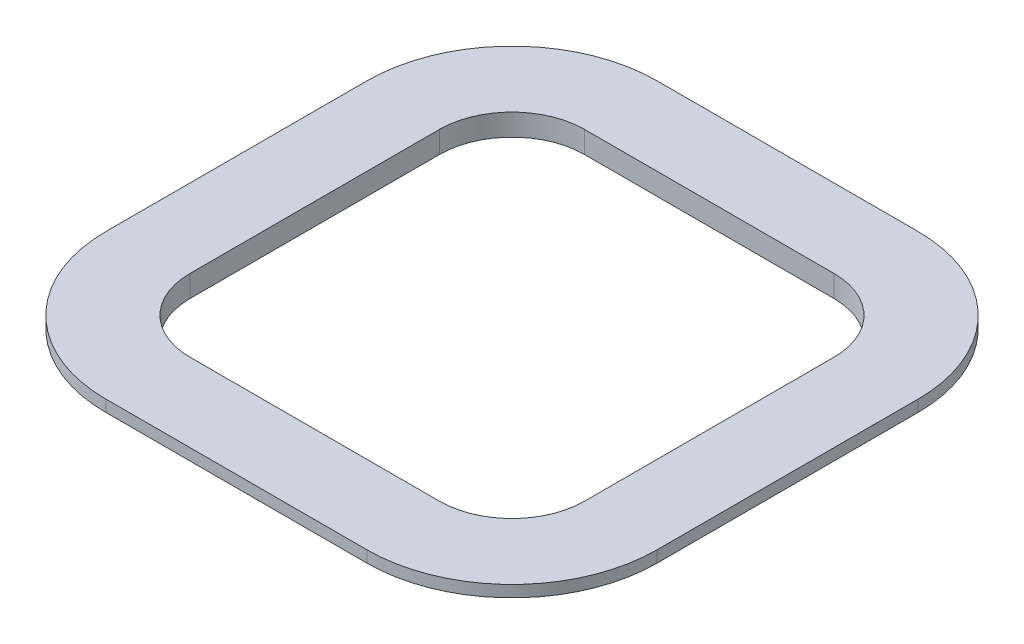
SolidWorks part; units mm, degrees
ref_plane "Front" through (0, 0, 0) normal (0, 0, 1) x (1, 0, 0)
ref_plane "Top" through (0, 0, 0) normal (0, 1, 0) x (1, 0, 0)
ref_plane "Right" through (0, 0, 0) normal (1, 0, 0) x (0, 0, -1)
sketch "Sketch1" plane through (0, 0, 0) normal (0, 1, 0) x (1, 0, 0)
  line L0 (-13.6, 13.6) -> (13.6, -13.6) construction
  line L1 (-19, 19) -> (19, 19)
  line L2 (-19, 19) -> (-19, -19)
  line L3 (-19, -19) -> (19, -19)
  line L4 (19, 19) -> (19, -19)
  line L5 (-13.6, 13.6) -> (13.6, 13.6)
  line L6 (-13.6, 13.6) -> (-13.6, -13.6)
  line L7 (-13.6, -13.6) -> (13.6, -13.6)
  line L8 (13.6, 13.6) -> (13.6, -13.6)
  line L9 (19, 19) -> (-19, -19) construction
  point P8 (0, 0)
  point P9 (0, 0)
  dimension "D1" = 38
  dimension "D2" = 27.2
extrude "Extrude1" add sketch "Sketch1" against normal blind 1.5
fillet "Fillet1" radius 5 4 edges at (13.6, -0.75, 13.6) (-13.6, -0.75, 13.6) (-13.6, -0.75, -13.6) (13.6, -0.75, -13.6)
fillet "Fillet2" radius 10 4 edges at (19, -0.75, 19) (19, -0.75, -19) (-19, -0.75, -19) (-19, -0.75, 19)
sketch "Sketch2" plane through (0, 0, 0) normal (0, 0, 1) x (1, 0, 0)
  line L0 (19, -0.8) -> (19, -1.5)
  line L1 (19, -1.5) -> (13.6, -1.5)
  line L2 (13.6, -1.5) -> (19, -0.8)
  dimension "D1" = 0.7
sketch "Sketch3" plane through (0, -1.5, 0) normal (0, -1, 0) x (1, 0, 0)
  line L4 (13.6, -8.6) -> (13.6, 8.6)
  line L5 (-8.6, -13.6) -> (8.6, -13.6)
  line L6 (-13.6, 8.6) -> (-13.6, -8.6)
  line L7 (8.6, 13.6) -> (-8.6, 13.6)
  line L8 (13.6, -8.6) -> (13.6, 8.6)
  line L9 (-8.6, -13.6) -> (8.6, -13.6)
  line L10 (-13.6, 8.6) -> (-13.6, -8.6)
  line L11 (8.6, 13.6) -> (-8.6, 13.6)
  arc A4 (8.6, -13.6) -> (13.6, -8.6) centre (8.6, -8.6) ccw
  arc A5 (-13.6, -8.6) -> (-8.6, -13.6) centre (-8.6, -8.6) ccw
  arc A6 (-8.6, 13.6) -> (-13.6, 8.6) centre (-8.6, 8.6) ccw
  arc A7 (13.6, 8.6) -> (8.6, 13.6) centre (8.6, 8.6) ccw
  arc A8 (8.6, -13.6) -> (13.6, -8.6) centre (8.6, -8.6) ccw
  arc A9 (-13.6, -8.6) -> (-8.6, -13.6) centre (-8.6, -8.6) ccw
  arc A10 (-8.6, 13.6) -> (-13.6, 8.6) centre (-8.6, 8.6) ccw
  arc A11 (13.6, 8.6) -> (8.6, 13.6) centre (8.6, 8.6) ccw
  dimension "D1" = 0
sketch "Sketch4" plane through (0, -1.5, 0) normal (0, -1, 0) x (1, 0, 0)
  line L0 (9, -19) -> (-9, -19) construction
  line L1 (-19, -9) -> (-19, 9) construction
  line L2 (-9, 19) -> (9, 19) construction
  line L3 (19, 9) -> (19, -9) construction
  line L4 (9, -19) -> (-9, -19)
  line L5 (-19, -9) -> (-19, 9)
  line L6 (-9, 19) -> (9, 19)
  line L7 (19, 9) -> (19, -9)
  arc A0 (9, -19) -> (19, -9) centre (9, -9) ccw construction
  arc A1 (-19, -9) -> (-9, -19) centre (-9, -9) ccw construction
  arc A2 (-9, 19) -> (-19, 9) centre (-9, 9) ccw construction
  arc A3 (19, 9) -> (9, 19) centre (9, 9) ccw construction
  arc A4 (9, -19) -> (19, -9) centre (9, -9) ccw
  arc A5 (-19, -9) -> (-9, -19) centre (-9, -9) ccw
  arc A6 (-9, 19) -> (-19, 9) centre (-9, 9) ccw
  arc A7 (19, 9) -> (9, 19) centre (9, 9) ccw
sweep "Cut-Sweep1" cut profiles "Sketch2" path "Sketch4"
